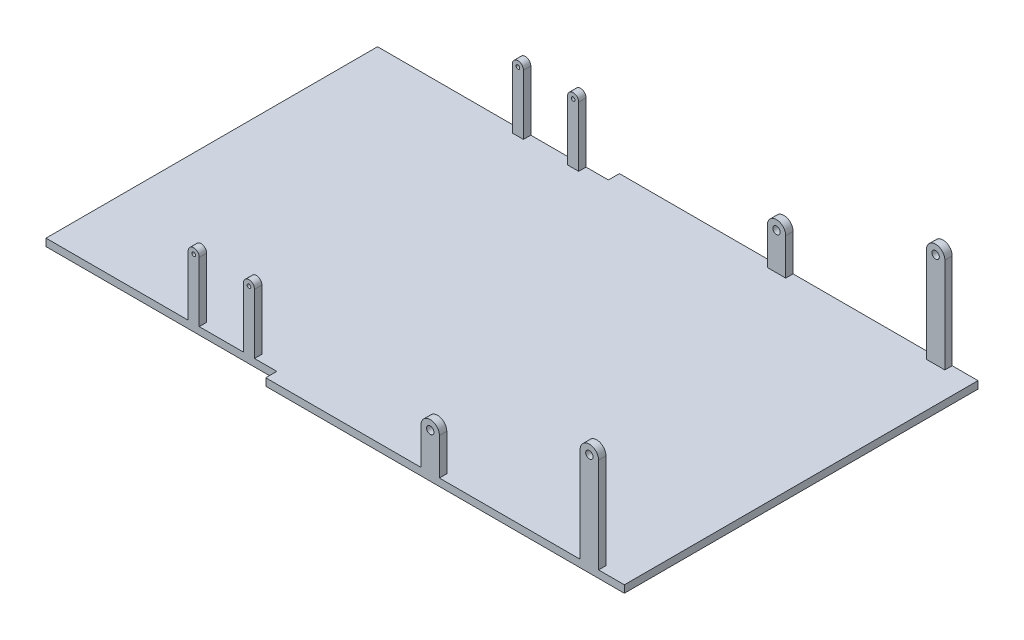
SolidWorks part; units mm, degrees
material "Alloy Steel"
ref_plane "Front Plane" through (0, 0, 0) normal (0, 0, 1) x (1, 0, 0)
ref_plane "Top Plane" through (0, 0, 0) normal (0, 1, 0) x (1, 0, 0)
ref_plane "Right Plane" through (0, 0, 0) normal (1, 0, 0) x (0, 0, -1)
sketch "Sketch1" plane through (0, 0, 0) normal (0, 1, 0) x (1, 0, 0)
  line L0 (-173.4223, 480) -> (-173.4223, 450)
  line L1 (-173.4223, 480) -> (800, 480)
  line L2 (-800, 450) -> (-800, -450)
  line L3 (-173.4223, -480) -> (800, -480)
  line L4 (800, 480) -> (800, -480)
  line L5 (0, 0) -> (800, -480) construction
  line L6 (-750, -450) -> (800, 480) construction
  line L7 (-173.4223, 450) -> (-800, 450)
  line L9 (0, 0) -> (-1738.6087, 0) construction
  line L11 (-173.4223, -450) -> (-800, -450)
  line L12 (-173.4223, -480) -> (-173.4223, -450)
  point P0 (0, 0)
  point P14 (-169.9618, 500)
  point P15 (-173.4223, 423.0416)
  point P16 (0, 0)
  dimension "D1" = 960
  dimension "D3" = 30
extrude "Boss-Extrude1" add sketch "Sketch1" against normal blind 20
sketch "Sketch2" plane through (0, 0, 480) normal (0, 0, 1) x (1, 0, 0)
  line L0 (298, 0) -> (298, 100)
  line L1 (-173.4223, 0) -> (800, 0) construction
  line L2 (248, 0) -> (248, 100)
  line L3 (730, 0) -> (730, 258.2)
  line L4 (680, 0) -> (680, 258.2)
  line L5 (800, -20) -> (800, 0) construction
  arc A0 (248, 100) -> (298, 100) centre (273, 100) cw
  arc A1 (680, 258.2) -> (730, 258.2) centre (705, 258.2) cw
  circle A2 centre (273, 100) radius 10
  circle A3 centre (705, 258.2) radius 10
  point P15 (-224, 208.8081)
  point P22 (-274, 0)
  point P30 (-386.9255, 0)
  point P31 (-438.4633, 0)
  point P32 (-462.25, 162.7)
  dimension "D1" = 25
  dimension "D2" = 25
  dimension "D6" = 20
  dimension "D7" = 20
  dimension "D3" = 70
  dimension "D4" = 432
  dimension "D5" = 158.2
  dimension "D8" = 100
extrude "Boss-Extrude2" add sketch "Sketch2" against normal blind 20
sketch "Sketch3" plane through (0, 0, 450) normal (0, 0, 1) x (1, 0, 0)
  line L6 (-234, 0) -> (-234, 162.7)
  line L7 (-264, 0) -> (-264, 162.7)
  line L8 (-384, 0) -> (-384, 162.7)
  line L9 (-414, 0) -> (-414, 162.7)
  arc A4 (-264, 162.7) -> (-234, 162.7) centre (-249, 162.7) cw
  circle A5 centre (-249, 162.7) radius 5
  arc A6 (-414, 162.7) -> (-384, 162.7) centre (-399, 162.7) cw
  circle A7 centre (-399, 162.7) radius 5
  point P15 (-224, 208.8081)
  point P22 (-274, 0)
  point P30 (-386.9255, 0)
  point P31 (-438.4633, 0)
  point P32 (-462.25, 162.7)
  dimension "D11" = 150
  dimension "D12" = 10
  dimension "D13" = 15
mirror "Mirror1" about plane through (0, 0, 0) normal (0, 0, 1) of bodies 102
extrude "Boss-Extrude3" add sketch "Sketch3" against normal blind 20
mirror "Mirror2" about plane through (0, 0, 0) normal (0, 0, 1) of "Boss-Extrude3"
equation "\"2cmcm\"=4"
